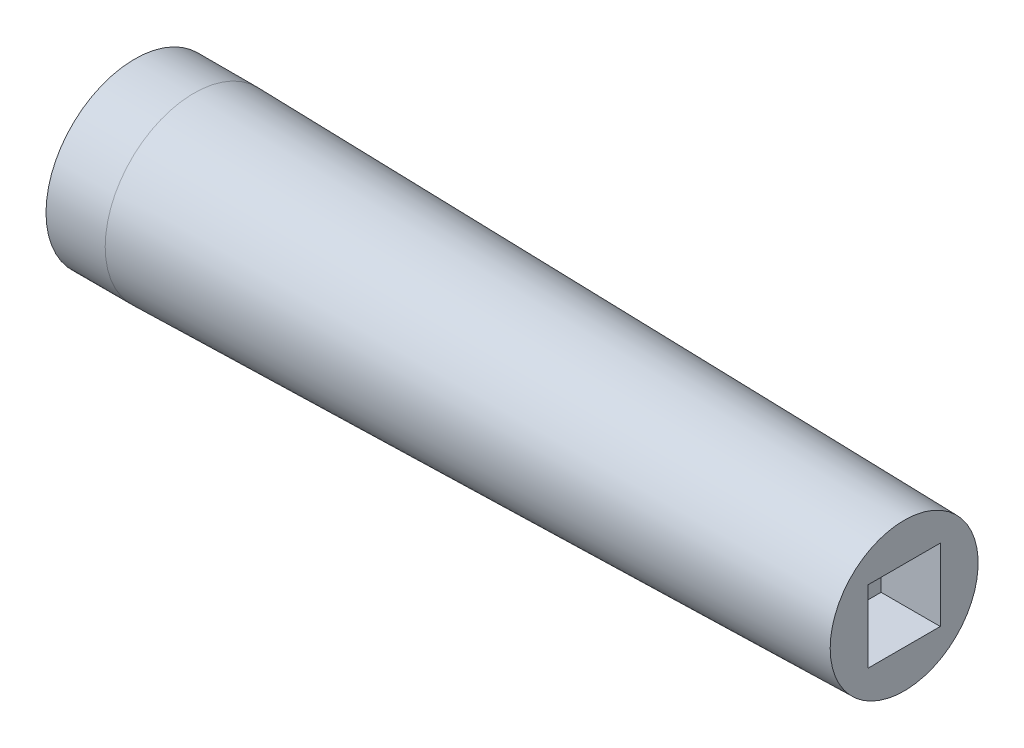
SolidWorks part; units mm, degrees
ref_plane "Front Plane" through (0, 0, 0) normal (0, 0, 1) x (1, 0, 0)
ref_plane "Top Plane" through (0, 0, 0) normal (0, 1, 0) x (1, 0, 0)
ref_plane "Right Plane" through (0, 0, 0) normal (1, 0, 0) x (0, 0, -1)
sketch "Sketch1" plane through (0, 0, 0) normal (0, 0, 1) x (1, 0, 0)
  line L0 (0, 0) -> (202.7583, 0) construction
  line L1 (0, 0) -> (165.1, 0)
  line L2 (165.1, 0) -> (165.1, 15.875)
  line L3 (165.1, 15.875) -> (12.7, 19.05)
  line L4 (12.7, 19.05) -> (0, 19.05)
  line L5 (0, 19.05) -> (0, 0)
  dimension "D1" = 165.1
  dimension "D2" = 15.875
  dimension "D3" = 19.05
  dimension "D4" = 12.7
revolve "Revolve1" add sketch "Sketch1" angle 360 about L0
sketch "Sketch2" plane through (165.1, 0, 0) normal (1, 0, 0) x (0, 0, -1)
  line L1 (-7.747, -7.747) -> (7.747, -7.747)
  line L2 (-7.747, -7.747) -> (-7.747, 7.747)
  line L3 (-7.747, 7.747) -> (7.747, 7.747)
  line L4 (7.747, -7.747) -> (7.747, 7.747)
  line L5 (-7.747, -7.747) -> (7.747, 7.747) construction
  line L6 (-7.747, 7.747) -> (7.747, -7.747) construction
  point P0 (0, 0)
  dimension "D1" = 15.494
extrude "Cut-Extrude1" cut sketch "Sketch2" against normal blind 12.7
